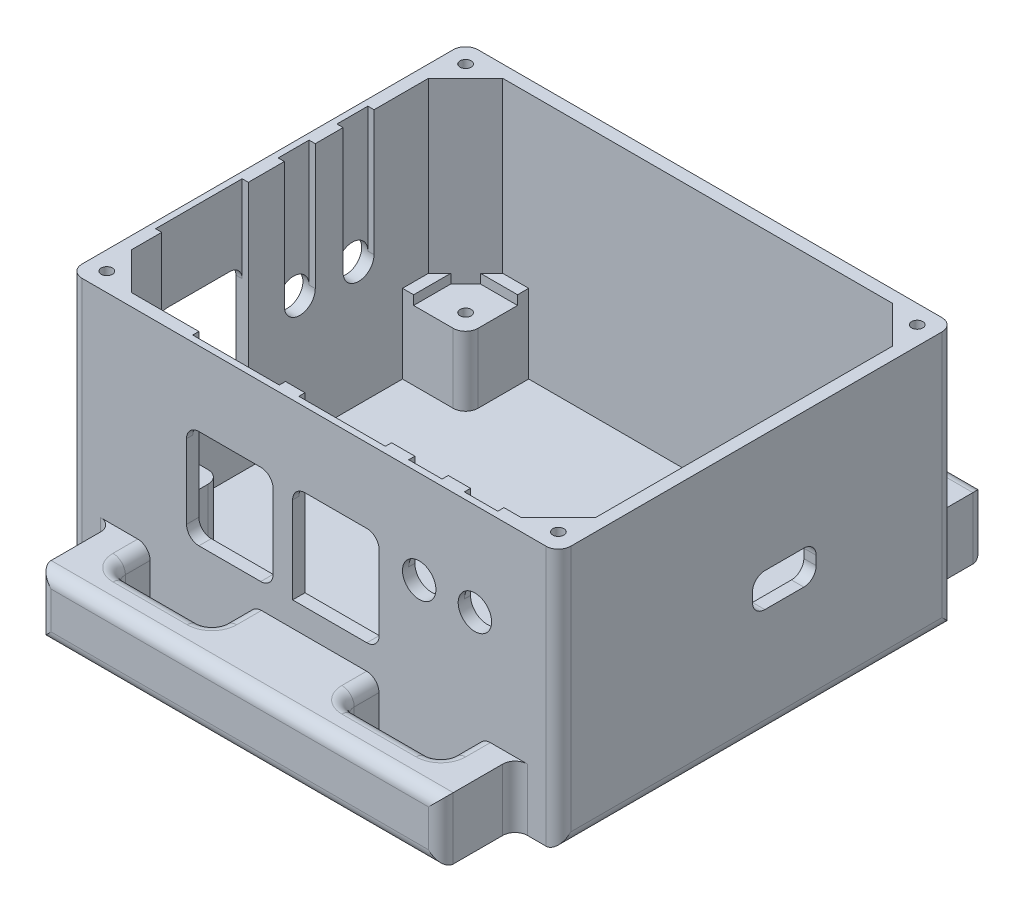
SolidWorks part; units mm, degrees
ref_plane "Front Plane" through (0, 0, 0) normal (0, 0, 1) x (1, 0, 0)
ref_plane "Top Plane" through (0, 0, 0) normal (0, 1, 0) x (1, 0, 0)
ref_plane "Right Plane" through (0, 0, 0) normal (1, 0, 0) x (0, 0, -1)
sketch "Sketch1" plane through (0, 0, 0) normal (0, 1, 0) x (1, 0, 0)
  line L1 (39.5, -32) -> (-39.5, -32)
  line L2 (39.5, -32) -> (39.5, 32)
  line L3 (39.5, 32) -> (-39.5, 32)
  line L4 (-39.5, -32) -> (-39.5, 32)
  line L5 (39.5, -32) -> (-39.5, 32) construction
  line L6 (39.5, 32) -> (-39.5, -32) construction
  point P0 (0, 0)
  dimension "D1" = 79
  dimension "D2" = 64
extrude "Boss-Extrude1" add sketch "Sketch1" along normal blind 2
sketch "Sketch2" plane through (0, 2, 0) normal (0, 1, 0) x (1, 0, 0)
  line L1 (-39.5, 32) -> (39.5, 32)
  line L2 (-39.5, 32) -> (-39.5, -32)
  line L3 (-39.5, -32) -> (39.5, -32)
  line L4 (39.5, 32) -> (39.5, -32)
  line L10 (37.5, -30) -> (-37.5, -30)
  line L14 (37.5, -30) -> (37.5, 30)
  line L15 (37.5, 30) -> (-37.5, 30)
  line L16 (-37.5, -30) -> (-37.5, 30)
  line L17 (37.5, -30) -> (-37.5, 30) construction
  line L18 (37.5, 30) -> (-37.5, -30) construction
  point P6 (0, 0)
  point P7 (0, 0)
  dimension "D1" = 2
  dimension "D2" = 2
extrude "Boss-Extrude2" add sketch "Sketch2" along normal blind 40
sketch "Sketch4" plane through (0, 2, 0) normal (0, 1, 0) x (1, 0, 0)
  line L0 (-37.5, 24) -> (-31.5, 30)
  line L1 (-37.5, 30) -> (-31.5, 30)
  line L2 (-37.5, 30) -> (-37.5, 24)
  line L5 (0, 0) -> (0, 30) construction
  line L6 (37.5, 30) -> (-37.5, 30) construction
  line L10 (0, 0) -> (-37.5, 0) construction
  line L11 (-37.5, 30) -> (-37.5, -30) construction
  line L12 (-37.5, -30) -> (-34.1667, -27.3333) construction
  line L13 (37.5, 30) -> (37.5, 24)
  line L14 (37.5, 30) -> (31.5, 30)
  line L15 (37.5, 24) -> (31.5, 30)
  line L16 (-37.5, -30) -> (-37.5, -24)
  line L17 (-37.5, -30) -> (-31.5, -30)
  line L18 (-37.5, -24) -> (-31.5, -30)
  line L19 (37.5, -30) -> (31.5, -30)
  line L20 (37.5, -24) -> (31.5, -30)
  line L21 (37.5, -30) -> (37.5, -24)
  dimension "D1" = 6
  dimension "D2" = 6
extrude "Boss-Extrude3" add sketch "Sketch4" along normal up to surface (40 mm away) up to face at (0, 42, 0)
sketch "Sketch3" plane through (0, 42, 0) normal (0, 1, 0) x (1, 0, 0)
  line L0 (39.5, 32) -> (-39.5, 32) construction
  line L1 (-39.5, 32) -> (-39.5, -32) construction
  line L3 (-39.5, -32) -> (39.5, -32) construction
  line L4 (39.5, -32) -> (39.5, 32) construction
  circle A0 centre (-36.5, 29) radius 0.9
  circle A1 centre (-36.5, -29) radius 0.9
  circle A2 centre (36.5, -29) radius 0.9
  circle A3 centre (36.5, 29) radius 0.9
  dimension "D1" = 1.8
  dimension "D2" = 3
  dimension "D3" = 3
  dimension "D4" = 1.8
  dimension "D5" = 3
  dimension "D6" = 3
  dimension "D7" = 1.8
  dimension "D8" = 3
  dimension "D9" = 3
  dimension "D10" = 1.8
  dimension "D11" = 3
  dimension "D12" = 3
extrude "Cut-Extrude2" cut sketch "Sketch3" against normal blind 10
sketch "Sketch5" plane through (0, 42, 0) normal (0, 1, 0) x (1, 0, 0)
  line L0 (-31.5, -30) -> (31.5, -30) construction
  line L1 (-20.6111, -30) -> (-6.6111, -30)
  line L2 (-20.6111, -30) -> (-20.6111, -31)
  line L3 (-20.6111, -31) -> (-6.6111, -31)
  line L4 (-6.6111, -30) -> (-6.6111, -31)
  line L5 (-37.5, 24) -> (-37.5, -24) construction
  line L6 (-3.4629, -30) -> (10.5371, -30)
  line L7 (-3.4629, -30) -> (-3.4629, -31)
  line L8 (-3.4629, -31) -> (10.5371, -31)
  line L9 (10.5371, -30) -> (10.5371, -31)
  line L10 (-37.5, -5.1206) -> (-38.5, -5.1206)
  line L11 (-37.5, -5.1206) -> (-37.5, -19.1206)
  line L12 (-37.5, -19.1206) -> (-38.5, -19.1206)
  line L13 (-38.5, -5.1206) -> (-38.5, -19.1206)
  dimension "D1" = 14
  dimension "D2" = 14
  dimension "D3" = 1
  dimension "D4" = 1
  dimension "D5" = 14
  dimension "D6" = 1
extrude "Cut-Extrude3" cut sketch "Sketch5" against normal blind 28
sketch "Sketch6" plane through (0, 0, 31) normal (0, 0, -1) x (-1, 0, 0)
  line L0 (6.6111, 14) -> (6.6111, 42) construction
  line L1 (20.6111, 14) -> (6.6111, 14)
  line L2 (20.6111, 14) -> (20.6111, 30)
  line L3 (20.6111, 30) -> (6.6111, 30)
  line L4 (6.6111, 14) -> (6.6111, 30)
  line L5 (3.4629, 14) -> (3.4629, 42) construction
  line L6 (-10.5371, 14) -> (3.4629, 14)
  line L7 (-10.5371, 14) -> (-10.5371, 30)
  line L8 (-10.5371, 30) -> (3.4629, 30)
  line L9 (3.4629, 14) -> (3.4629, 30)
  dimension "D1" = 16
  dimension "D2" = 16
extrude "Cut-Extrude4" cut sketch "Sketch6" against normal blind 2
sketch "Sketch7" plane through (-38.5, 0, 0) normal (1, 0, 0) x (0, 0, -1)
  line L0 (-19.1206, 14) -> (-19.1206, 42) construction
  line L1 (-5.1206, 14) -> (-19.1206, 14)
  line L2 (-5.1206, 14) -> (-5.1206, 30)
  line L3 (-5.1206, 30) -> (-19.1206, 30)
  line L4 (-19.1206, 14) -> (-19.1206, 30)
  dimension "D1" = 16
extrude "Cut-Extrude5" cut sketch "Sketch7" against normal blind 2
sketch "Sketch8" plane through (0, 42, 0) normal (0, 1, 0) x (1, 0, 0)
  line L0 (-37.5, 24) -> (-37.5, -5.1206) construction
  line L1 (-37.5, 15.4397) -> (-38.5, 15.4397)
  line L2 (-37.5, 15.4397) -> (-37.5, 9.4397)
  line L3 (-37.5, 9.4397) -> (-38.5, 9.4397)
  line L4 (-38.5, 15.4397) -> (-38.5, 9.4397)
  line L6 (-37.5, 6) -> (-38.5, 6)
  line L7 (-37.5, 6) -> (-37.5, 0)
  line L8 (-37.5, 0) -> (-38.5, 0)
  line L9 (-38.5, 6) -> (-38.5, 0)
  dimension "D1" = 6
  dimension "D2" = 6
  dimension "D3" = 1
  dimension "D4" = 1
sketch "Sketch9" plane through (-37.5, 0, 0) normal (1, 0, 0) x (0, 0, -1)
  line L0 (24, 42) -> (-5.1206, 42) construction
  line L1 (24, 42) -> (24, 2) construction
  line L2 (15.4397, 42) -> (9.4397, 42) construction
  line L4 (0.7, 21.71) -> (0.7, 42)
  line L5 (0.7, 42) -> (5.7, 42)
  line L6 (5.7, 21.71) -> (5.7, 42)
  line L8 (10.2, 21.71) -> (10.2, 42)
  line L9 (10.2, 42) -> (15.2, 42)
  line L10 (15.2, 21.71) -> (15.2, 42)
  arc A0 (10.2, 21.71) -> (15.2, 21.71) centre (12.7, 21.71) ccw
  arc A1 (0.7, 21.71) -> (5.7, 21.71) centre (3.2, 21.71) ccw
  dimension "D1" = 5
  dimension "D2" = 5
  dimension "D3" = 20.29
  dimension "D4" = 20.29
  dimension "D6" = 11.3
  dimension "D5" = 9.5
extrude "Cut-Extrude7" cut sketch "Sketch9" against normal blind 1
sketch "Sketch10" plane through (-38.5, 0, 0) normal (1, 0, 0) x (0, 0, -1)
  circle A0 centre (3.2, 21.71) radius 2.5
  circle A1 centre (12.7, 21.71) radius 2.5
extrude "Cut-Extrude8" cut sketch "Sketch10" against normal blind 3
sketch "Sketch11" plane through (0, 0, 32) normal (0, 0, 1) x (1, 0, 0)
  line L0 (-39.5, 42) -> (39.5, 42) construction
  line L1 (39.5, 42) -> (39.5, 0) construction
  circle A0 centre (17, 27) radius 2.7
  circle A2 centre (26, 27) radius 2.7
  dimension "D1" = 5.4
  dimension "D2" = 5.4
  dimension "D3" = 15
  dimension "D4" = 15
  dimension "D5" = 9
  dimension "D6" = 13.5
extrude "Cut-Extrude9" cut sketch "Sketch11" against normal blind 3
sketch "Sketch12" plane through (0, 0, 30) normal (0, 0, -1) x (-1, 0, 0)
  line L0 (-10.5371, 42) -> (-31.5, 42) construction
  line L1 (-28.7, 27) -> (-23.3, 27)
  line L2 (-28.7, 27) -> (-28.7, 42)
  line L3 (-28.7, 42) -> (-23.3, 42)
  line L4 (-23.3, 27) -> (-23.3, 42)
  line L6 (-19.7, 27) -> (-14.3, 27)
  line L7 (-19.7, 27) -> (-19.7, 42)
  line L8 (-19.7, 42) -> (-14.3, 42)
  line L9 (-14.3, 27) -> (-14.3, 42)
  circle A0 centre (-26, 27) radius 2.7 construction
  circle A1 centre (-17, 27) radius 2.7 construction
extrude "Cut-Extrude10" cut sketch "Sketch12" against normal blind 1
sketch "Sketch13" plane through (37.5, 0, 0) normal (-1, 0, 0) x (0, 0, 1)
  line L0 (24, 2) -> (-24, 2) construction
  line L1 (-9.67, 22.89) -> (0.63, 22.89)
  line L2 (-9.67, 22.89) -> (-9.67, 17.44)
  line L3 (-9.67, 17.44) -> (0.63, 17.44)
  line L4 (0.63, 22.89) -> (0.63, 17.44)
  line L5 (-32, 42) -> (-32, 0) construction
  dimension "D1" = 5.45
  dimension "D2" = 10.3
  dimension "D3" = 15.44
  dimension "D4" = 22.33
extrude "Cut-Extrude11" cut sketch "Sketch13" against normal blind 2
fillet "Fillet1" radius 2 3 edges at (-39.5, 0, 0) (-39.5, 21, -32) (-39.5, 21, 32)
fillet "Fillet2" radius 2 3 edges at (39.5, 0, 0) (39.5, 21, -32) (39.5, 21, 32)
fillet "Fillet5" radius 2 1 edges at (-20.6111, 14, 31)
fillet "Fillet6" radius 2 1 edges at (-6.6111, 30, 31.5)
fillet "Fillet7" radius 2 1 edges at (-20.6111, 30, 31.5)
fillet "Fillet8" radius 2 1 edges at (-6.6111, 14, 31)
fillet "Fillet9" radius 2 1 edges at (-3.4629, 30, 31.5)
fillet "Fillet10" radius 2 1 edges at (10.5371, 30, 31.5)
fillet "Fillet11" radius 2 1 edges at (10.5371, 14, 31)
fillet "Fillet12" radius 2 1 edges at (-38.5, 14, 5.1206)
fillet "Fillet13" radius 2 1 edges at (-38.5, 14, 19.1206)
fillet "Fillet14" radius 2 1 edges at (-39, 30, 19.1206)
fillet "Fillet15" radius 2 1 edges at (-39, 30, 5.1206)
fillet "Fillet16" radius 2 1 edges at (38.5, 17.44, -9.67)
fillet "Fillet17" radius 2 1 edges at (38.5, 22.89, 0.63)
fillet "Fillet18" radius 2 1 edges at (38.5, 22.89, -9.67)
fillet "Fillet19" radius 2 1 edges at (38.5, 17.44, 0.63)
sketch "Sketch14" plane through (0, 2, 0) normal (0, 1, 0) x (1, 0, 0)
  line L0 (-31.5, -30) -> (31.5, -30) construction
  line L1 (-27.3, -30) -> (-37.5, -30)
  line L2 (-27.3, -30) -> (-27.3, -19.8)
  line L3 (-27.3, -19.8) -> (-37.5, -19.8)
  line L4 (-37.5, -30) -> (-37.5, -19.8)
  line L5 (-37.5, 24) -> (-37.5, -24) construction
  line L6 (31.5, 30) -> (-31.5, 30) construction
  line L7 (-37.5, 19.8) -> (-27.3, 19.8)
  line L8 (-37.5, 19.8) -> (-37.5, 30)
  line L9 (-37.5, 30) -> (-27.3, 30)
  line L10 (-27.3, 19.8) -> (-27.3, 30)
  line L11 (37.5, -24) -> (37.5, 24) construction
  line L12 (28.3, -30) -> (37.5, -30)
  line L13 (28.3, -30) -> (28.3, -19.8)
  line L14 (28.3, -19.8) -> (37.5, -19.8)
  line L15 (37.5, -30) -> (37.5, -19.8)
  line L17 (28.3, 30) -> (37.5, 30)
  line L18 (28.3, 30) -> (28.3, 19.8)
  line L19 (28.3, 19.8) -> (37.5, 19.8)
  line L20 (37.5, 30) -> (37.5, 19.8)
  dimension "D1" = 10.2
  dimension "D2" = 10.2
  dimension "D3" = 10.2
  dimension "D4" = 10.2
  dimension "D5" = 10.2
  dimension "D6" = 9.2
  dimension "D7" = 9.2
  dimension "D8" = 10.2
extrude "Boss-Extrude5" add sketch "Sketch14" along normal blind 11.2
sketch "Sketch15" plane through (0, 13.2, 0) normal (0, 1, 0) x (1, 0, 0)
  line L0 (37.5, -24) -> (37.5, -19.8) construction
  line L1 (28.3, -30) -> (31.5, -30) construction
  line L2 (37.5, 19.8) -> (37.5, 24) construction
  line L3 (31.5, 30) -> (28.3, 30) construction
  line L4 (-37.5, -19.8) -> (-37.5, -24) construction
  line L5 (-31.5, -30) -> (-27.3, -30) construction
  line L6 (-27.3, 30) -> (-31.5, 30) construction
  line L7 (-37.5, 24) -> (-37.5, 19.8) construction
  circle A0 centre (-30.5, -23) radius 0.9
  circle A1 centre (-30.5, 23) radius 0.9
  circle A2 centre (31.5, 23) radius 0.9
  circle A3 centre (31.5, -23) radius 0.9
  dimension "D1" = 1.8
  dimension "D2" = 1.8
  dimension "D3" = 1.8
  dimension "D4" = 1.8
  dimension "D5" = 6
  dimension "D6" = 7
  dimension "D7" = 6
  dimension "D8" = 7
  dimension "D9" = 7
  dimension "D10" = 7
  dimension "D11" = 7
  dimension "D12" = 7
extrude "Cut-Extrude12" cut sketch "Sketch15" against normal blind 10
sketch "Sketch17" plane through (0, 13.2, 0) normal (0, 1, 0) x (1, 0, 0)
  line L0 (-37.5, 24) -> (-35.7, 25.8)
  line L1 (-37.5, -19.8) -> (-35.7, -19.8)
  line L2 (-37.5, -19.8) -> (-37.5, -24)
  line L4 (-35.7, -19.8) -> (-35.7, -25.8)
  line L5 (-27.3, -30) -> (-31.5, -30)
  line L6 (-27.3, -30) -> (-27.3, -28.2)
  line L7 (-27.3, -28.2) -> (-33.3, -28.2)
  line L9 (-37.5, 19.8) -> (-35.7, 19.8)
  line L10 (-37.5, 19.8) -> (-37.5, 24)
  line L12 (-35.7, 19.8) -> (-35.7, 25.8)
  line L13 (-27.3, 30) -> (-31.5, 30)
  line L14 (-27.3, 30) -> (-27.3, 28.2)
  line L15 (-27.3, 28.2) -> (-33.3, 28.2)
  line L17 (37.5, 19.8) -> (36.7, 19.8)
  line L18 (37.5, 19.8) -> (37.5, 24)
  line L20 (36.7, 19.8) -> (36.7, 24.8)
  line L21 (28.3, 30) -> (31.5, 30)
  line L22 (28.3, 30) -> (28.3, 28.2)
  line L23 (28.3, 28.2) -> (33.3, 28.2)
  line L25 (28.3, -30) -> (31.5, -30)
  line L26 (28.3, -30) -> (28.3, -28.2)
  line L27 (28.3, -28.2) -> (33.3, -28.2)
  line L29 (37.5, -19.8) -> (36.7, -19.8)
  line L30 (37.5, -19.8) -> (37.5, -24)
  line L32 (36.7, -19.8) -> (36.7, -24.8)
  line L33 (-31.5, -30) -> (-33.3, -28.2)
  line L34 (31.5, -30) -> (33.3, -28.2)
  line L35 (31.5, 30) -> (33.3, 28.2)
  line L36 (-35.7, -25.8) -> (-37.5, -24)
  line L37 (-33.3, 28.2) -> (-31.5, 30)
  line L38 (36.7, 24.8) -> (37.5, 24)
  line L39 (36.7, -24.8) -> (37.5, -24)
  dimension "D1" = 0.8
  dimension "D2" = 1.8
  dimension "D3" = 0.8
  dimension "D4" = 1.8
  dimension "D5" = 1.8
  dimension "D6" = 1.8
  dimension "D7" = 1.8
  dimension "D8" = 1.8
extrude "Boss-Extrude6" add sketch "Sketch17" along normal blind 1.5
fillet "Fillet20" radius 2 1 edges at (-27.3, 7.6, 19.8)
fillet "Fillet21" radius 2 1 edges at (-27.3, 7.6, -19.8)
fillet "Fillet22" radius 2 1 edges at (28.3, 7.6, -19.8)
fillet "Fillet23" radius 2 1 edges at (28.3, 7.6, 19.8)
sketch "Sketch18" plane through (0, 0, 32) normal (0, 0, 1) x (1, 0, 0)
  line L0 (-37.5, 0) -> (37.5, 0) construction
  line L1 (-32.5, 0) -> (32.5, 0)
  line L2 (-32.5, 0) -> (-32.5, 10)
  line L3 (-32.5, 10) -> (32.5, 10)
  line L4 (32.5, 0) -> (32.5, 10)
  line L5 (-37.5, 42) -> (-37.5, 0) construction
  line L6 (37.5, 0) -> (37.5, 42) construction
  dimension "D1" = 5
  dimension "D2" = 5
  dimension "D3" = 10
extrude "Boss-Extrude7" add sketch "Sketch18" along normal blind 12
sketch "Sketch19" plane through (0, 10, 0) normal (0, 1, 0) x (1, 0, 0)
  line L0 (32.5, -32) -> (-32.5, -32) construction
  line L1 (-26.5, -32) -> (-10.5, -32)
  line L2 (-26.5, -32) -> (-26.5, -38)
  line L3 (-26.5, -38) -> (-10.5, -38)
  line L4 (-10.5, -32) -> (-10.5, -38)
  line L5 (-32.5, -44) -> (-32.5, -32) construction
  line L6 (10.5, -32) -> (26.5, -32)
  line L7 (10.5, -32) -> (10.5, -38)
  line L8 (10.5, -38) -> (26.5, -38)
  line L9 (26.5, -32) -> (26.5, -38)
  line L10 (32.5, -44) -> (32.5, -32) construction
  dimension "D1" = 16
  dimension "D2" = 16
  dimension "D3" = 6
  dimension "D4" = 6
  dimension "D5" = 6
  dimension "D6" = 6
extrude "Cut-Extrude13" cut sketch "Sketch19" against normal blind 12
fillet "Fillet24" radius 2 8 edges at (-26.5, 0, 35) (-10.5, 0, 35) (-10.5, 10, 35) (-26.5, 10, 35) (-18.5, 0, 38) (-10.5, 5, 38) (-18.5, 10, 38) (-26.5, 5, 38)
fillet "Fillet25" radius 2 8 edges at (10.5, 0, 35) (26.5, 0, 35) (26.5, 10, 35) (10.5, 10, 35) (18.5, 0, 38) (26.5, 5, 38) (18.5, 10, 38) (10.5, 5, 38)
fillet "Fillet26" radius 2 4 edges at (0, 10, 44) (32.5, 5, 44) (0, 0, 44) (-32.5, 5, 44)
fillet "Fillet27" radius 2 1 edges at (-32.5, 5, 32)
fillet "Fillet28" radius 2 1 edges at (32.5, 5, 32)
ref_plane "Plane2" through (0, 0, 0) normal (0, 0, -1) x (-1, 0, 0)
mirror "Mirror8" about plane through (0, 0, 0) normal (0, 0, -1) of "Fillet25", "Cut-Extrude13", "Boss-Extrude7", "Fillet24", "Fillet26"
fillet "Fillet29" radius 2 1 edges at (32.5, 5, -32)
fillet "Fillet30" radius 2 1 edges at (-32.5, 5, -32)
equation "\"esquina\"= 8"
